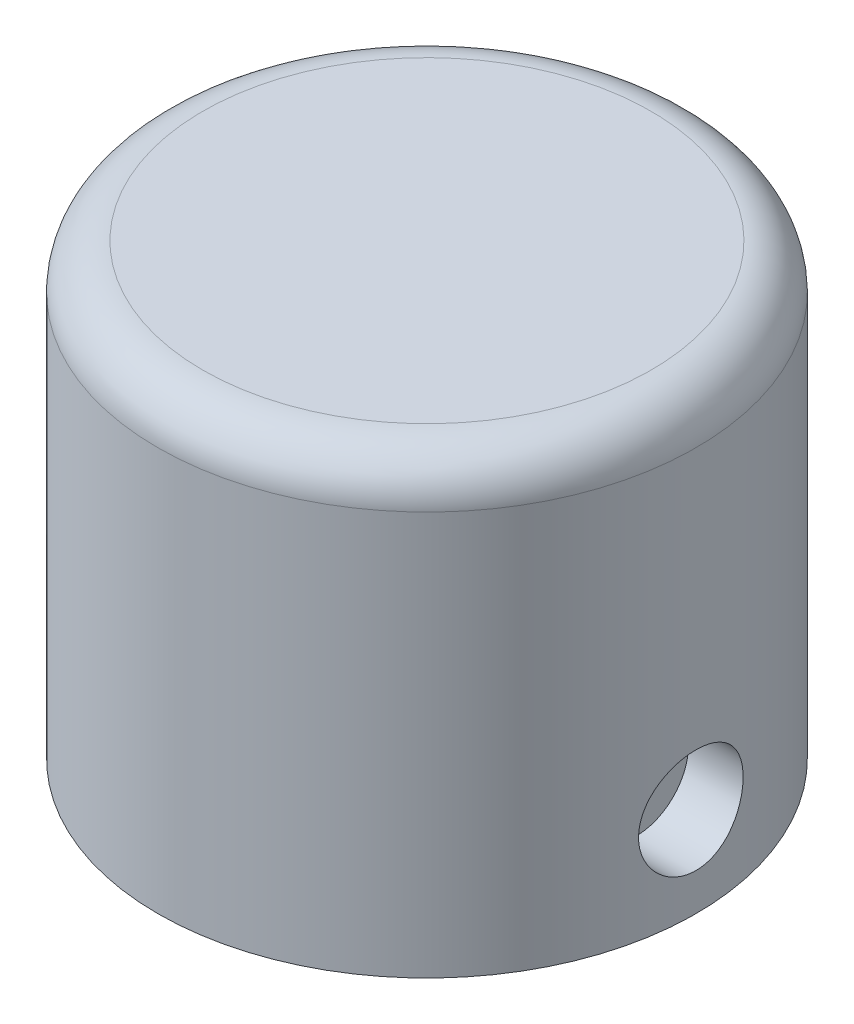
SolidWorks part; units mm, degrees
ref_plane "Спереди" through (0, 0, 0) normal (0, 0, 1) x (1, 0, 0)
ref_plane "Сверху" through (0, 0, 0) normal (0, 1, 0) x (1, 0, 0)
ref_plane "Справа" through (0, 0, 0) normal (1, 0, 0) x (0, 0, -1)
sketch "Sketch1" plane through (0, 0, 0) normal (0, 1, 0) x (1, 0, 0)
  circle A0 centre (0, 0) radius 18
  dimension "D1" = 36
extrude "Boss-Extrude1" add sketch "Sketch1" along normal blind 30
fillet "Fillet1" radius 3 1 edges at (0, 30, 18)
sketch "Sketch2" plane through (0, 0, 0) normal (0, -1, 0) x (1, 0, 0)
  line L1 (-5, 5) -> (5, 5)
  line L2 (-5, 5) -> (-5, -5)
  line L3 (-5, -5) -> (5, -5)
  line L4 (5, 5) -> (5, -5)
  line L5 (-5, 5) -> (5, -5) construction
  line L6 (-5, -5) -> (5, 5) construction
  point P0 (0, 0)
  dimension "D1" = 10
extrude "Cut-Extrude1" cut sketch "Sketch2" against normal blind 25
sketch "Sketch3" plane through (5, 0, 0) normal (-1, 0, 0) x (0, 0, 1)
  line L0 (0, 0) -> (0, 6) construction
  line L1 (-5, 0) -> (5, 0) construction
  circle A0 centre (0, 6) radius 1.6
  dimension "D1" = 3.2
  dimension "D2" = 6
extrude "Cut-Extrude2" cut sketch "Sketch3" against normal through all both and the other way through all
sketch "Sketch4" plane through (5, 0, 0) normal (-1, 0, 0) x (0, 0, 1)
  circle A0 centre (0, 6) radius 3.5
  dimension "D1" = 7
extrude "Cut-Extrude3" cut sketch "Sketch4" against normal blind 20 from offset 9 offset against normal yes
sketch "Sketch5" plane through (-5, 0, 0) normal (1, 0, 0) x (0, 0, -1)
  line L0 (-5, 25) -> (-5, 0) construction
  line L1 (-2.8146, 7.625) -> (-2.8146, 4.375)
  line L2 (-2.8146, 4.375) -> (0, 2.75)
  line L3 (0, 2.75) -> (2.8146, 4.375)
  line L4 (2.8146, 4.375) -> (2.8146, 7.625)
  line L5 (2.8146, 7.625) -> (0, 9.25)
  line L6 (0, 9.25) -> (-2.8146, 7.625)
  circle A0 centre (0, 6) radius 3.25 construction
  dimension "D1" = 6.5
extrude "Cut-Extrude4" cut sketch "Sketch5" against normal blind 16 from offset 8
